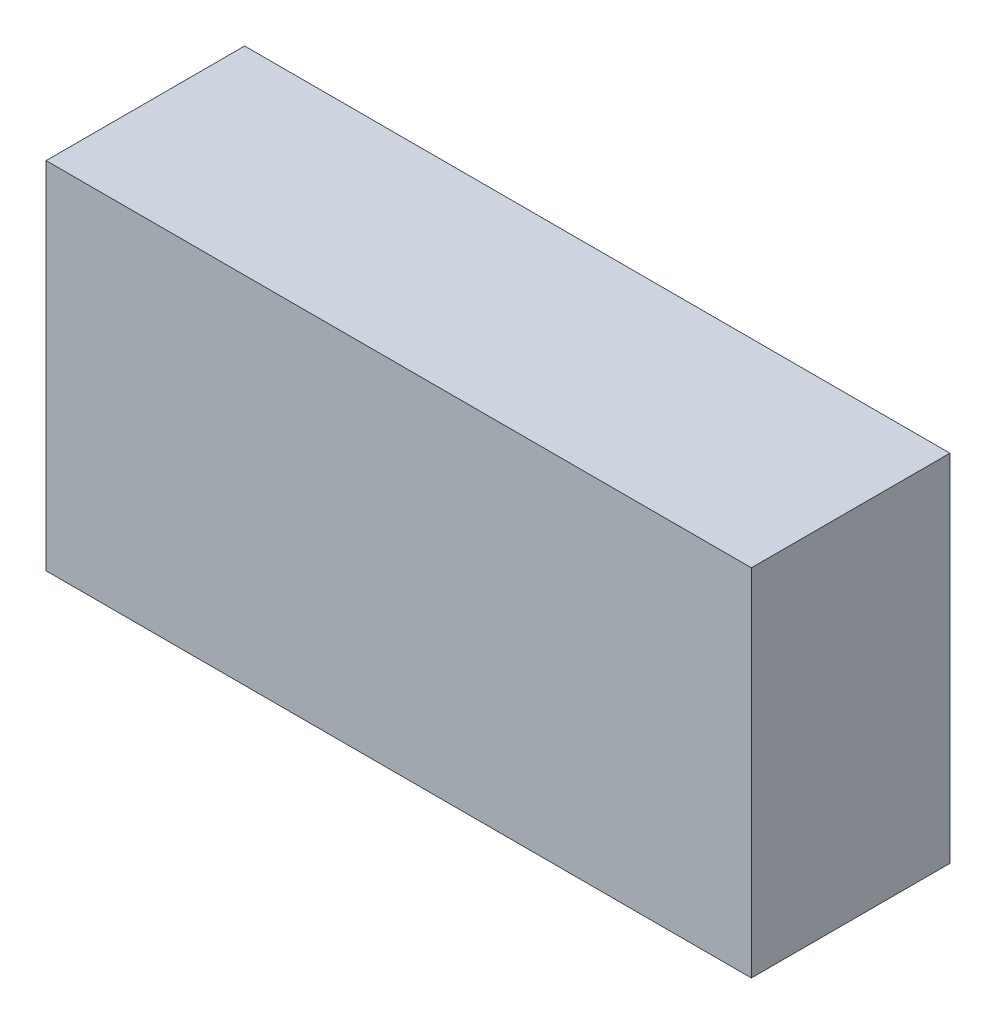
SolidWorks part; units mm, degrees
ref_plane "Спереди" through (0, 0, 0) normal (0, 0, 1) x (1, 0, 0)
ref_plane "Сверху" through (0, 0, 0) normal (0, 1, 0) x (1, 0, 0)
ref_plane "Справа" through (0, 0, 0) normal (1, 0, 0) x (0, 0, -1)
other "Configuration Table"
sketch "Эскиз1" plane through (0, 0, 0) normal (0, 1, 0) x (1, 0, 0)
  line L1 (0, 0) -> (135, 0)
  line L2 (0, 0) -> (0, 38)
  line L3 (0, 38) -> (135, 38)
  line L4 (135, 0) -> (135, 38)
  line L5 (67.5, 38) -> (67.5, 0) construction
  line L6 (0, 19) -> (135, 19) construction
  point P232 (67.5, 19)
  dimension "D1" = 135
  dimension "D2" = 38
extrude "Корпус" add sketch "Эскиз1" along normal blind 68
sketch "Эскиз2" plane through (0, 0, 0) normal (0, -1, 0) x (1, 0, 0)
  line L0 (0, -38) -> (0, 0) construction
  line L1 (2, -1.6) -> (41, -1.6)
  line L2 (2, -1.6) -> (2, -16.6)
  line L3 (2, -16.6) -> (41, -16.6)
  line L4 (41, -1.6) -> (41, -16.6)
  line L5 (21.5, -16.6) -> (21.5, -1.6) construction
  line L6 (2, -9.1) -> (41, -9.1) construction
  line L7 (48, -1.6) -> (87, -1.6)
  line L8 (48, -1.6) -> (48, -16.6)
  line L9 (48, -16.6) -> (87, -16.6)
  line L10 (87, -1.6) -> (87, -16.6)
  line L11 (67.5, -16.6) -> (67.5, -1.6) construction
  line L12 (48, -9.1) -> (87, -9.1) construction
  line L13 (94, -1.6) -> (133, -1.6)
  line L14 (94, -1.6) -> (94, -16.6)
  line L15 (94, -16.6) -> (133, -16.6)
  line L16 (133, -1.6) -> (133, -16.6)
  line L17 (113.5, -16.6) -> (113.5, -1.6) construction
  line L18 (94, -9.1) -> (133, -9.1) construction
  line L19 (48, -19.6) -> (87, -19.6)
  line L20 (48, -19.6) -> (48, -34.6)
  line L21 (48, -34.6) -> (87, -34.6)
  line L22 (87, -19.6) -> (87, -34.6)
  line L23 (67.5, -34.6) -> (67.5, -19.6) construction
  line L24 (48, -27.1) -> (87, -27.1) construction
  line L25 (94, -19.6) -> (133, -19.6)
  line L26 (94, -19.6) -> (94, -34.6)
  line L27 (94, -34.6) -> (133, -34.6)
  line L28 (133, -19.6) -> (133, -34.6)
  line L29 (113.5, -34.6) -> (113.5, -19.6) construction
  line L30 (94, -27.1) -> (133, -27.1) construction
  line L31 (2, -19.6) -> (41, -19.6)
  line L32 (2, -19.6) -> (2, -34.6)
  line L33 (2, -34.6) -> (41, -34.6)
  line L34 (41, -19.6) -> (41, -34.6)
  line L35 (21.5, -34.6) -> (21.5, -19.6) construction
  line L36 (2, -27.1) -> (41, -27.1) construction
  line L37 (135, 0) -> (135, -38) construction
  line L38 (0, 0) -> (135, 0) construction
  point P16 (67.5, -9.1)
  point P25 (113.5, -9.1)
  point P34 (67.5, -27.1)
  point P43 (113.5, -27.1)
  point P52 (21.5, -27.1)
  point P292 (21.5, -9.1)
  dimension "D1" = 2
  dimension "D2" = 39
  dimension "D3" = 15
  dimension "D6" = 2
  dimension "D7" = 1.6
  dimension "D4" = 3
  dimension "D5" = 2
extrude "Вырез-Вытянуть1" cut sketch "Эскиз2" against normal blind 66
sketch "Эскиз4" plane through (0, 0, 0) normal (0, -1, 0) x (1, 0, 0)
  line L0 (41, -16.6) -> (41, -1.6) construction
  line L1 (41, -5.7894) -> (94, -5.7894)
  line L2 (41, -5.7894) -> (41, -15.2176)
  line L3 (41, -15.2176) -> (94, -15.2176)
  line L4 (94, -5.7894) -> (94, -15.2176)
  line L5 (67.5, -15.2176) -> (67.5, -5.7894) construction
  line L6 (41, -10.5035) -> (94, -10.5035) construction
  line L7 (94, -1.6) -> (94, -16.6) construction
  point P776 (67.5, -10.5035)
extrude "Вырез-Вытянуть2" cut sketch "Эскиз4" against normal blind 66
ref_plane "Плоскость1" through (41, 0, -19.6) normal (0, 0, 1) x (1, 0, 0)
sketch "Эскиз6" plane through (0, 0, 0) normal (0, -1, 0) x (1, 0, 0)
  line L0 (41, -34.6) -> (41, -19.6) construction
  line L1 (41, -23.2117) -> (94, -23.2117)
  line L2 (41, -23.2117) -> (41, -33.3649)
  line L3 (41, -33.3649) -> (94, -33.3649)
  line L4 (94, -23.2117) -> (94, -33.3649)
  line L5 (67.5, -33.3649) -> (67.5, -23.2117) construction
  line L6 (41, -28.2883) -> (94, -28.2883) construction
  line L7 (94, -19.6) -> (94, -34.6) construction
  point P348 (67.5, -28.2883)
extrude "Вырез-Вытянуть3" cut sketch "Эскиз6" against normal blind 66
sketch "Эскиз7" plane through (0, 0, 0) normal (0, -1, 0) x (1, 0, 0)
  line L0 (2, -16.6) -> (41, -16.6) construction
  line L1 (7.6517, -16.6) -> (37.9858, -16.6)
  line L2 (7.6517, -16.6) -> (7.6517, -19.6)
  line L3 (7.6517, -19.6) -> (37.9858, -19.6)
  line L4 (37.9858, -16.6) -> (37.9858, -19.6)
  line L5 (22.8187, -19.6) -> (22.8187, -16.6) construction
  line L6 (7.6517, -18.1) -> (37.9858, -18.1) construction
  line L7 (41, -19.6) -> (2, -19.6) construction
  line L8 (48, -16.6) -> (87, -16.6) construction
  line L9 (50.2834, -16.6) -> (84.0334, -16.6)
  line L10 (50.2834, -16.6) -> (50.2834, -19.6)
  line L11 (50.2834, -19.6) -> (84.0334, -19.6)
  line L12 (84.0334, -16.6) -> (84.0334, -19.6)
  line L13 (67.1584, -19.6) -> (67.1584, -16.6) construction
  line L14 (50.2834, -18.1) -> (84.0334, -18.1) construction
  line L15 (87, -19.6) -> (48, -19.6) construction
  line L16 (94, -16.6) -> (133, -16.6) construction
  line L17 (96.6043, -16.6) -> (127.6216, -16.6)
  line L18 (96.6043, -16.6) -> (96.6043, -19.6)
  line L19 (96.6043, -19.6) -> (127.6216, -19.6)
  line L20 (127.6216, -16.6) -> (127.6216, -19.6)
  line L21 (112.1129, -19.6) -> (112.1129, -16.6) construction
  line L22 (96.6043, -18.1) -> (127.6216, -18.1) construction
  line L23 (133, -19.6) -> (94, -19.6) construction
  point P168 (22.8187, -18.1)
  point P249 (67.1584, -18.1)
  point P282 (112.1129, -18.1)
extrude "Вырез-Вытянуть4" cut sketch "Эскиз7" against normal blind 66
sketch "Эскиз11" plane through (0, 0, 0) normal (0, -1, 0) x (1, 0, 0)
  line L0 (2, -34.6) -> (41, -34.6) construction
  line L1 (7.7884, -34.6) -> (36.6194, -34.6)
  line L2 (7.7884, -34.6) -> (7.7884, -38)
  line L3 (7.7884, -38) -> (36.6194, -38)
  line L4 (36.6194, -34.6) -> (36.6194, -38)
  line L5 (22.2039, -38) -> (22.2039, -34.6) construction
  line L6 (7.7884, -36.3) -> (36.6194, -36.3) construction
  line L7 (135, -38) -> (0, -38) construction
  line L8 (94, -34.6) -> (133, -34.6) construction
  line L9 (51.3765, -36.6) -> (83.3502, -36.6)
  line L10 (51.3765, -36.6) -> (51.3765, -38)
  line L11 (51.3765, -38) -> (83.3502, -38)
  line L12 (83.3502, -36.6) -> (83.3502, -38)
  line L13 (67.3634, -38) -> (67.3634, -36.6) construction
  line L14 (51.3765, -37.3) -> (83.3502, -37.3) construction
  line L15 (127.2116, -34.6) -> (97.9707, -34.6)
  line L16 (127.2116, -34.6) -> (127.2116, -38)
  line L17 (127.2116, -38) -> (97.9707, -38)
  line L18 (97.9707, -34.6) -> (97.9707, -38)
  line L19 (112.5912, -38) -> (112.5912, -34.6) construction
  line L20 (127.2116, -36.3) -> (97.9707, -36.3) construction
  point P244 (67.3634, -37.3)
  point P265 (112.5912, -36.3)
  point P284 (22.2039, -36.3)
extrude "Вырез-Вытянуть6" cut sketch "Эскиз11" against normal blind 63
sketch "Эскиз12" plane through (0, 0, 0) normal (0, -1, 0) x (1, 0, 0)
  line L0 (83.3502, -36.6) -> (51.3765, -36.6) construction
  line L1 (51.3765, -36.6) -> (83.3502, -36.6)
  line L2 (51.3765, -36.6) -> (51.3765, -34.6)
  line L3 (51.3765, -34.6) -> (83.3502, -34.6)
  line L4 (83.3502, -36.6) -> (83.3502, -34.6)
  line L5 (67.3634, -34.6) -> (67.3634, -36.6) construction
  line L6 (51.3765, -35.6) -> (83.3502, -35.6) construction
  line L7 (48, -34.6) -> (87, -34.6) construction
  point P188 (67.3634, -35.6)
extrude "Вырез-Вытянуть7" cut sketch "Эскиз12" against normal blind 63
